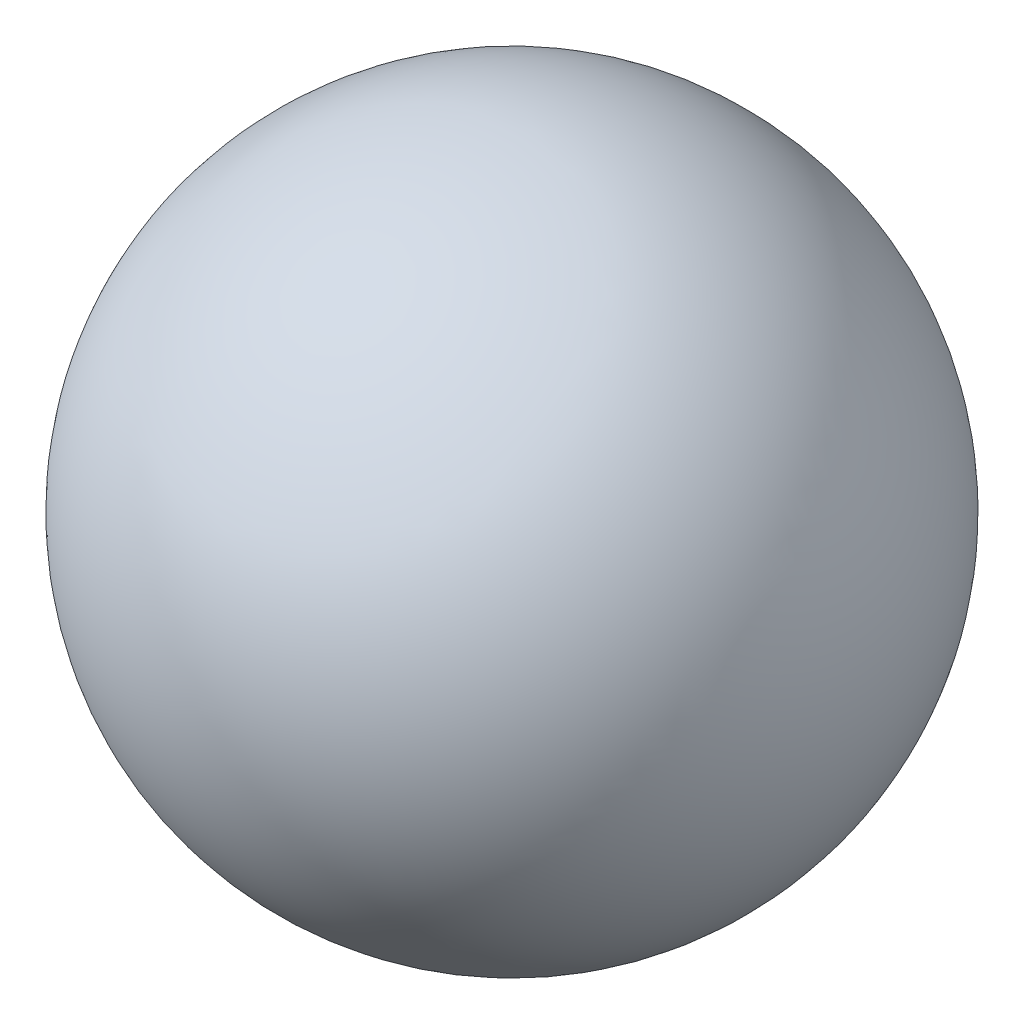
SolidWorks part; units mm, degrees
ref_plane "Front Plane" through (0, 0, 0) normal (0, 0, 1) x (1, 0, 0)
ref_plane "Top Plane" through (0, 0, 0) normal (0, 1, 0) x (1, 0, 0)
ref_plane "Right Plane" through (0, 0, 0) normal (1, 0, 0) x (0, 0, -1)
sketch "Sketch2" plane through (0, 0, 0) normal (0, 0, 1) x (1, 0, 0)
  line L0 (-66.4512, 0) -> (66.4512, 0)
  arc A1 (66.4512, 0) -> (-66.4512, 0) centre (0, 0) ccw
  point P5 (0, 0)
revolve "Revolve1" add sketch "Sketch2" angle 360 about L0
